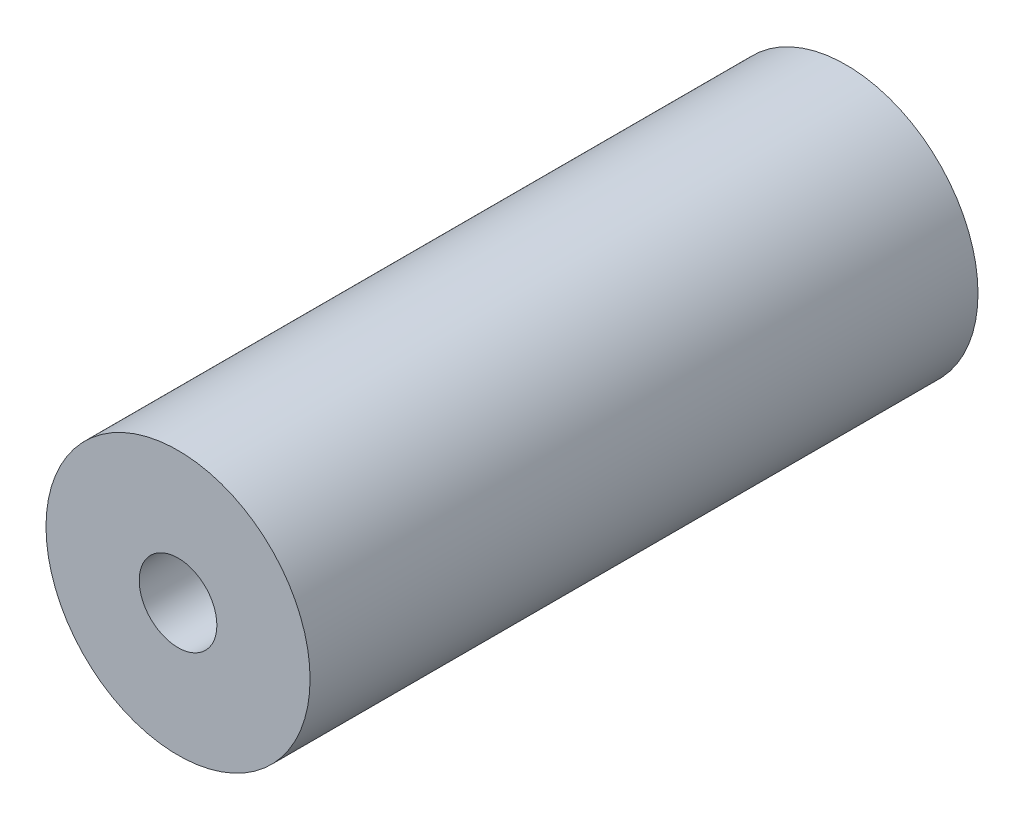
SolidWorks part; units mm, degrees
ref_plane "Alzado" through (0, 0, 0) normal (0, 0, 1) x (1, 0, 0)
ref_plane "Planta" through (0, 0, 0) normal (0, 1, 0) x (1, 0, 0)
ref_plane "Vista lateral" through (0, 0, 0) normal (1, 0, 0) x (0, 0, -1)
sketch "Croquis1" plane through (0, 0, 0) normal (0, 0, 1) x (1, 0, 0)
  circle A0 centre (0, 0) radius 17
  circle A1 centre (0, 0) radius 5
  dimension "D1" = 34
  dimension "D2" = 10
extrude "Saliente-Extruir1" add sketch "Croquis1" along normal mid plane 86
